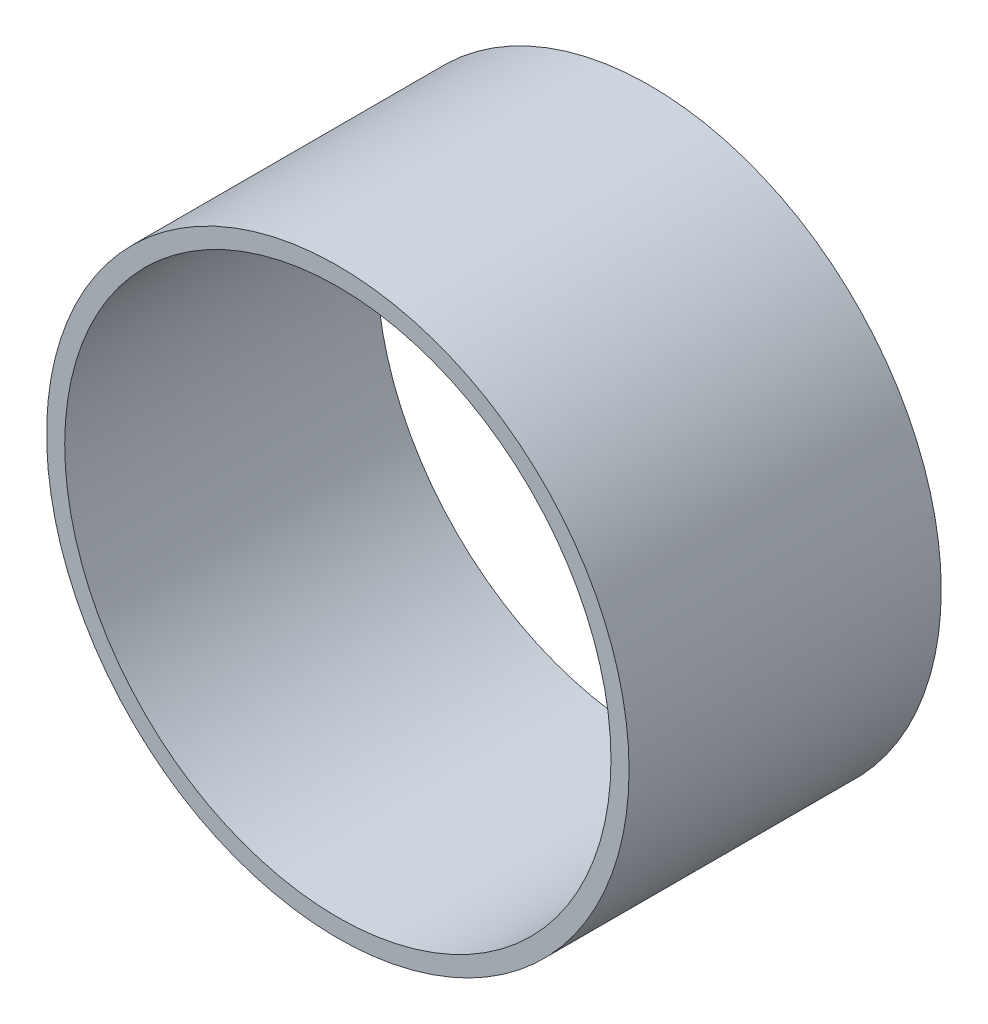
SolidWorks part; units mm, degrees
ref_plane "Front Plane" through (0, 0, 0) normal (0, 0, 1) x (1, 0, 0)
ref_plane "Top Plane" through (0, 0, 0) normal (0, 1, 0) x (1, 0, 0)
ref_plane "Right Plane" through (0, 0, 0) normal (1, 0, 0) x (0, 0, -1)
sketch "Sketch1" plane through (0, 0, 0) normal (0, 0, 1) x (1, 0, 0)
  circle A0 centre (0, 0) radius 22.225
  circle A1 centre (0, 0) radius 23.6982
extrude "Boss-Extrude" add sketch "Sketch1" along normal blind 25.4 contours A1
